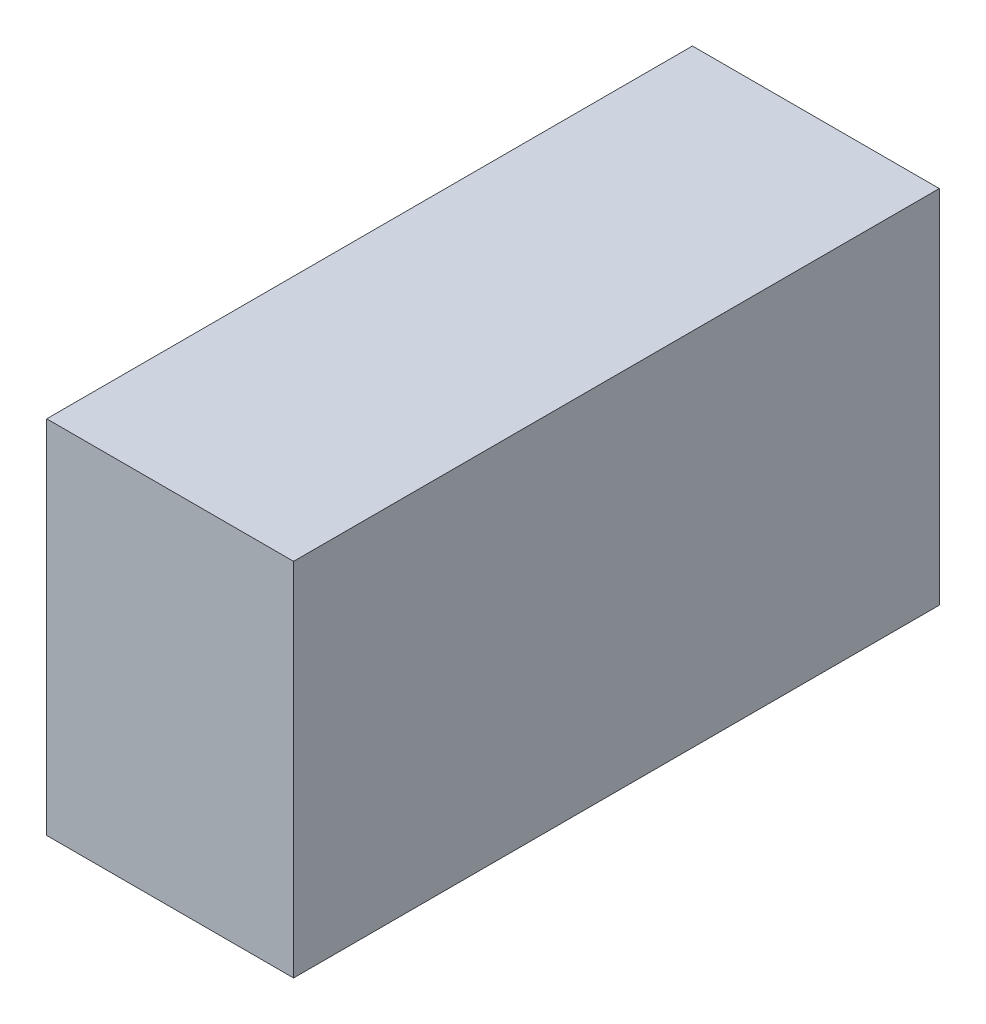
SolidWorks part; units mm, degrees
ref_plane "Front Plane" through (0, 0, 0) normal (0, 0, 1) x (1, 0, 0)
ref_plane "Top Plane" through (0, 0, 0) normal (0, 1, 0) x (1, 0, 0)
ref_plane "Right Plane" through (0, 0, 0) normal (1, 0, 0) x (0, 0, -1)
sketch "Sketch1" plane through (0, 0, 0) normal (0, 1, 0) x (1, 0, 0)
  line L1 (-65, -170) -> (65, -170)
  line L2 (-65, -170) -> (-65, 170)
  line L3 (-65, 170) -> (65, 170)
  line L4 (65, -170) -> (65, 170)
  line L5 (-65, -170) -> (65, 170) construction
  line L6 (-65, 170) -> (65, -170) construction
  point P0 (0, 0)
  dimension "D1" = 130
  dimension "D2" = 340
extrude "Boss-Extrude1" add sketch "Sketch1" along normal blind 190
equation "\"PCLength\"= 130mm'Length across I/O from PS to GPU"
equation "\"PCWidth\"= 340mm'Distance of longest part parallel to GPU(ussually GPU)"
equation "\"PCHeight\"= 190mm'Tallest point with mobo laying flat"
equation "\"WallThickness\"= 9mm'Thickness of each outer tank wall"
equation "\"ThermoBarrierThickness\"= 6mm'Thickness of barrier between hot side and cold side"
equation "\"HotSideGap\"= 26mm'Space in the hot side for a pump"
equation "\"PCClearance\"= 30mm'Clearance from top of tank to top of PC"
equation "\"RadiatorHeight\"= 275mm'Final Height from ground of radiators"
equation "\"D1@Sketch1\"=\"PCLength\""
equation "\"D2@Sketch1\"=\"PCWidth\""
equation "\"D1@Boss-Extrude1\"=\"PCHeight\""
